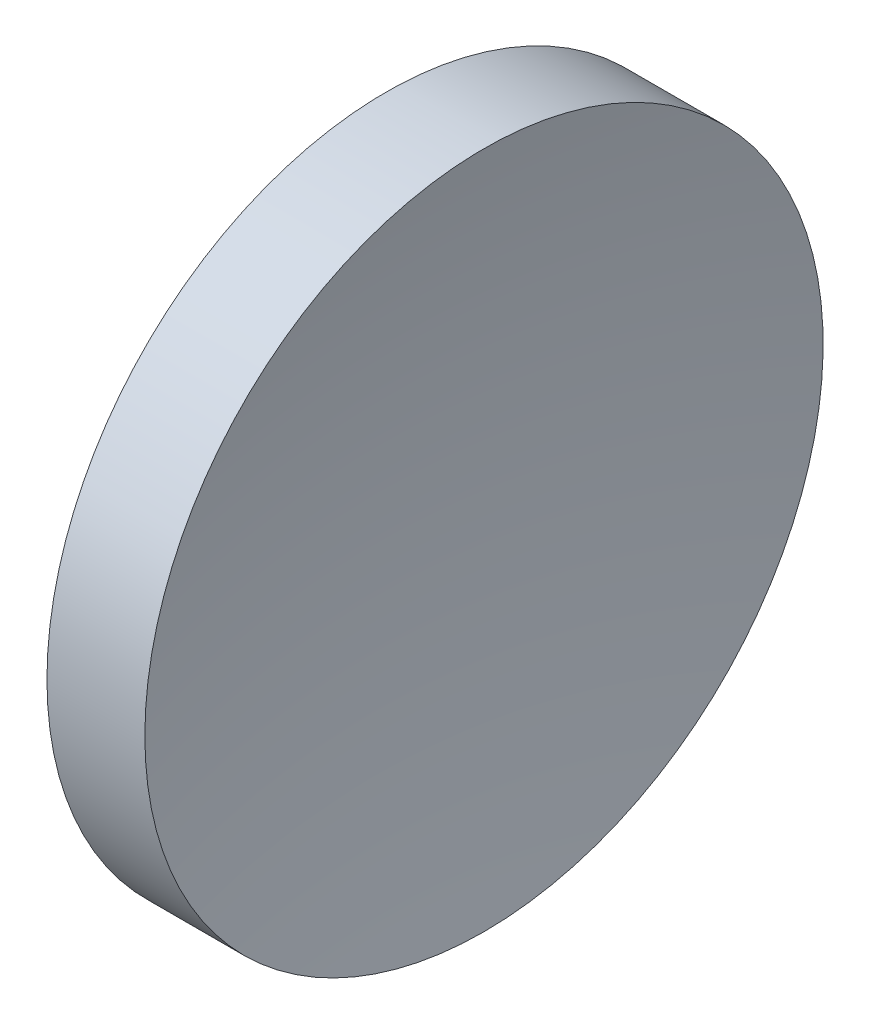
SolidWorks part; units mm, degrees
ref_plane "前视基准面" through (0, 0, 0) normal (0, 0, 1) x (1, 0, 0)
ref_plane "上视基准面" through (0, 0, 0) normal (0, 1, 0) x (1, 0, 0)
ref_plane "右视基准面" through (0, 0, 0) normal (1, 0, 0) x (0, 0, -1)
sketch "草图1" plane through (0, 0, 0) normal (0, 0, 1) x (1, 0, 0)
  line L0 (103.2333, 65.2215) -> (130.0478, 65.2215) construction
  line L1 (115.0646, 82.2215) -> (119.9723, 82.2215)
  line L2 (118.3146, 65.2215) -> (115.0646, 65.2215)
  line L4 (115.0646, 65.2215) -> (115.0646, 82.2215)
  arc A0 (119.9723, 82.2215) -> (118.3146, 65.2215) centre (206.3146, 65.2215) ccw
revolve "旋转1" add sketch "草图1" angle 360 about L0
